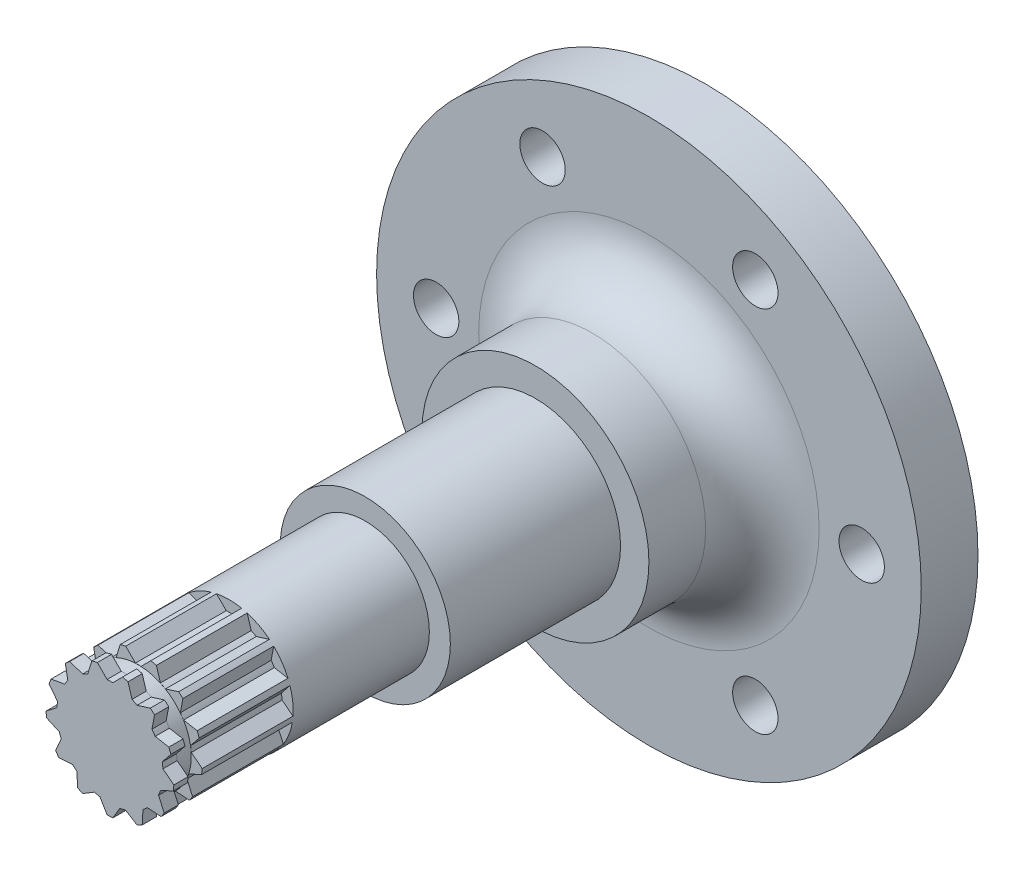
SolidWorks part; units mm, degrees
ref_plane "Front Plane" through (0, 0, 0) normal (0, 0, 1) x (1, 0, 0)
ref_plane "Top Plane" through (0, 0, 0) normal (0, 1, 0) x (1, 0, 0)
ref_plane "Right Plane" through (0, 0, 0) normal (1, 0, 0) x (0, 0, -1)
sketch "Sketch1" plane through (0, 0, 0) normal (0, 0, 1) x (1, 0, 0)
  circle A0 centre (0, 0) radius 48
  dimension "D1" = 96
extrude "Boss-Extrude2" add sketch "Sketch1" along normal blind 10
sketch "Sketch5" plane through (0, 0, 0) normal (0, 0, 1) x (1, 0, 0)
  circle A0 centre (0, 0) radius 20
  dimension "D1" = 40
extrude "Boss-Extrude3" add sketch "Sketch5" along normal blind 30
sketch "Sketch8" plane through (0, 0, 30) normal (0, 0, 1) x (1, 0, 0)
  circle A0 centre (0, 0) radius 15
  dimension "D1" = 30
extrude "Boss-Extrude4" add sketch "Sketch8" along normal blind 30
sketch "Sketch9" plane through (0, 0, 60) normal (0, 0, 1) x (1, 0, 0)
  circle A0 centre (0, 0) radius 11.3
  dimension "D1" = 22.6
extrude "Boss-Extrude5" add sketch "Sketch9" along normal blind 45
sketch "Sketch10" plane through (0, 0, 10) normal (0, 0, 1) x (1, 0, 0)
  circle A0 centre (0, 0) radius 37.5
  circle A1 centre (-37.5, 0) radius 4
  circle A2 centre (-18.75, 32.476) radius 4
  circle A3 centre (18.75, 32.476) radius 4
  circle A4 centre (37.5, 0) radius 4
  circle A5 centre (18.75, -32.476) radius 4
  circle A6 centre (-18.75, -32.476) radius 4
  dimension "D1" = 75
  dimension "D2" = 8
  dimension "D3" = 6
extrude "Cut-Extrude1" cut sketch "Sketch10" against normal blind 45 contours A1 | A2 | A3 | A4 | A5 | A6
fillet "Fillet1" radius 10 1 edges at (20, 0, 10)
sketch "Sketch11" plane through (0, 0, 105) normal (0, 0, 1) x (1, 0, 0)
  line L0 (0, -1000) -> (0, 49000) construction
  line L1 (0, 0) -> (-0.5008, -11.2889) construction
  line L2 (0, 0) -> (-1.7532, -9.1994) construction
  line L3 (0, 0) -> (-2.7224, -8.9606) construction
  line L4 (0, 0) -> (-4.8042, -10.2279) construction
  line L5 (0, 0) -> (-5.6892, -9.7633) construction
  line L6 (-0.5008, -11.2889) -> (-1.7532, -9.1994)
  line L7 (-1.7532, -9.1994) -> (-2.7224, -8.9606)
  line L8 (-2.7224, -8.9606) -> (-4.8042, -10.2279)
  line L9 (-4.8042, -10.2279) -> (-5.6892, -9.7633)
  line L10 (-5.6896, -9.7631) -> (-5.8276, -7.3309)
  line L11 (-5.8276, -7.3309) -> (-6.5748, -6.669)
  line L12 (-6.5748, -6.669) -> (-9.007, -6.8237)
  line L13 (-9.007, -6.8237) -> (-9.5748, -6.0011)
  line L14 (-9.5751, -6.0007) -> (-8.5669, -3.783)
  line L15 (-8.5669, -3.783) -> (-8.9209, -2.8497)
  line L16 (-8.9209, -2.8497) -> (-11.1465, -1.8564)
  line L17 (-11.1465, -1.8564) -> (-11.2669, -0.8641)
  line L18 (-11.267, -0.8636) -> (-9.3437, 0.6316)
  line L19 (-9.3437, 0.6316) -> (-9.2234, 1.6225)
  line L20 (-9.2234, 1.6225) -> (-10.7324, 3.5363)
  line L21 (-10.7324, 3.5363) -> (-10.3779, 4.4709)
  line L22 (-10.3777, 4.4713) -> (-7.9799, 4.9015)
  line L23 (-7.9799, 4.9015) -> (-7.4129, 5.723)
  line L24 (-7.4129, 5.723) -> (-7.8597, 8.1188)
  line L25 (-7.8597, 8.1188) -> (-7.1114, 8.7817)
  line L26 (-7.1111, 8.7819) -> (-4.788, 8.0485)
  line L27 (-4.788, 8.0485) -> (-3.9042, 8.5124)
  line L28 (-3.9042, 8.5124) -> (-3.1864, 10.8414)
  line L29 (-3.1864, 10.8414) -> (-2.2158, 11.0806)
  line L30 (-2.2154, 11.0807) -> (-0.4993, 9.3517)
  line L31 (-0.4993, 9.3517) -> (0.4989, 9.3517)
  line L32 (0.4989, 9.3517) -> (2.2169, 11.0804)
  line L33 (2.2169, 11.0804) -> (3.1874, 10.8411)
  line L34 (3.1878, 10.841) -> (3.9038, 8.5125)
  line L35 (3.9038, 8.5125) -> (4.7877, 8.0487)
  line L36 (4.7877, 8.0487) -> (7.1123, 8.781)
  line L37 (7.1123, 8.781) -> (7.8604, 8.1181)
  line L38 (7.8608, 8.1178) -> (7.4127, 5.7233)
  line L39 (7.4127, 5.7233) -> (7.9797, 4.9018)
  line L40 (7.9797, 4.9018) -> (10.3783, 4.4699)
  line L41 (10.3783, 4.4699) -> (10.7327, 3.5353)
  line L42 (10.7329, 3.5349) -> (9.2233, 1.6229)
  line L43 (9.2233, 1.6229) -> (9.3437, 0.6319)
  line L44 (9.3437, 0.6319) -> (11.2668, -0.8651)
  line L45 (11.2668, -0.8651) -> (11.1463, -1.8574)
  line L46 (11.1462, -1.8579) -> (8.921, -2.8493)
  line L47 (8.921, -2.8493) -> (8.5671, -3.7827)
  line L48 (8.5671, -3.7827) -> (9.5743, -6.002)
  line L49 (9.5743, -6.002) -> (9.0064, -6.8246)
  line L50 (9.0061, -6.825) -> (6.575, -6.6687)
  line L51 (6.575, -6.6687) -> (5.8279, -7.3307)
  line L52 (5.8279, -7.3307) -> (5.6883, -9.7639)
  line L53 (5.6883, -9.7639) -> (4.8032, -10.2284)
  line L54 (4.8028, -10.2285) -> (2.7228, -8.9604)
  line L55 (2.7228, -8.9604) -> (1.7536, -9.1994)
  line L56 (1.7536, -9.1994) -> (0.4993, -11.289)
  line L57 (0.4993, -11.289) -> (-0.5003, -11.2889)
  circle A0 centre (0, 0) radius 11.3
  circle A1 centre (0, 0) radius 9.365
  circle M61 centre (0, 0) radius 11.3
  dimension "D1" = 22.6
  dimension "D2" = 18.73
  dimension "D3" = 2.54
  dimension "D4" = 10.79
  dimension "D5" = 16.9
  dimension "D6" = 25.16
  dimension "D7" = 30.23
  dimension "D8" = 13
extrude "Cut-Extrude12" cut sketch "Sketch11" against normal blind 21 contours A1 L24 L22 M61 | A1 L28 L26 M61 | A1 L32 L30 M61 | A1 L36 L34 M61 | A1 L40 L38 M61 | A1 L44 L42 M61 | A1 L48 L46 M61 | A1 L52 L50 M61 | A1 L56 L54 M61 | A1 L8 L6 M61 | A1 L12 L10 M61 | A1 L16 L14 M61 | A1 L20 L18 M61
ref_plane "Plane8" through (0, 0, 100) normal (0, 0, -1) x (-1, 0, 0)
sketch "Sketch17" plane through (0, 0, 100) normal (0, 0, -1) x (-1, 0, 0)
  circle A0 centre (0, 0) radius 9.35
  circle A1 centre (0, 0) radius 12.9103
  dimension "D1" = 18.7
extrude "Cut-Extrude13" cut sketch "Sketch17" against normal blind 2.5
